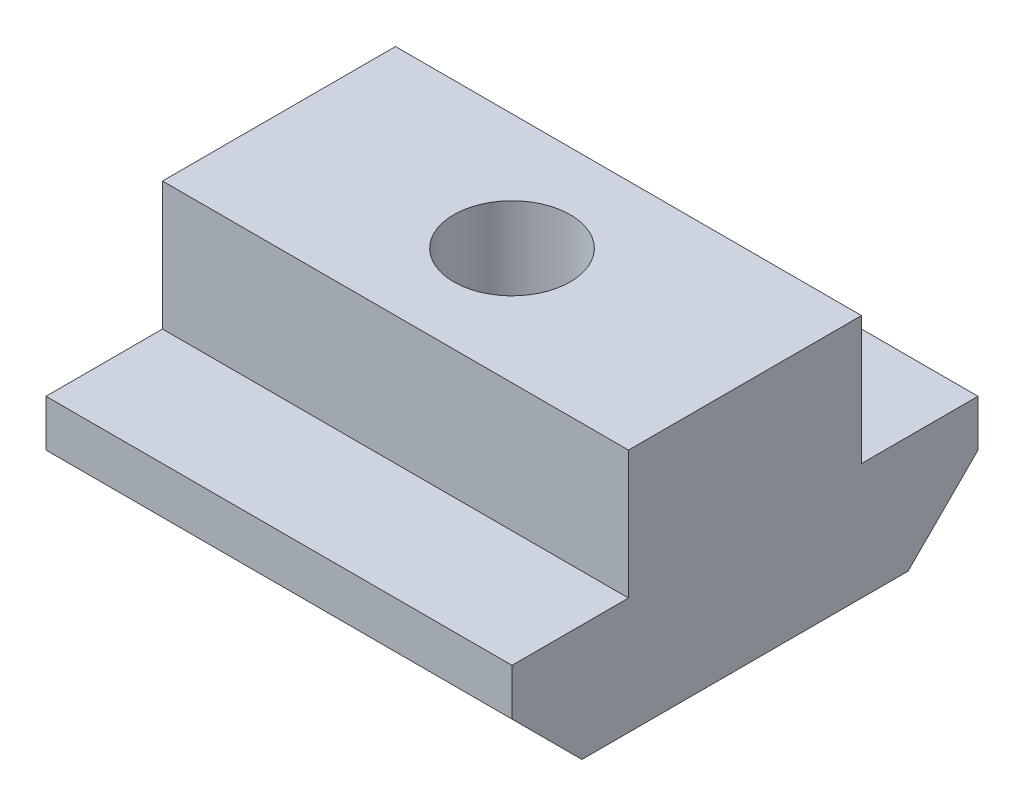
SolidWorks part; units mm, degrees
ref_plane "Спереди" through (0, 0, 0) normal (0, 0, 1) x (1, 0, 0)
ref_plane "Сверху" through (0, 0, 0) normal (0, 1, 0) x (1, 0, 0)
ref_plane "Справа" through (0, 0, 0) normal (1, 0, 0) x (0, 0, -1)
sketch "Эскиз1" plane through (0, 0, 0) normal (1, 0, 0) x (0, 0, -1)
  line L0 (0, 9.2317) -> (-5, 9.2317) construction
  line L1 (-7, -5.25) -> (7, -5.25)
  line L2 (-10, -2.25) -> (-10, -0.25)
  line L3 (-5, 5.25) -> (5, 5.25)
  line L4 (10, -2.25) -> (10, -0.25)
  line L5 (-10, -2.25) -> (-7, -5.25)
  line L6 (7, -5.25) -> (10, -2.25)
  line L7 (-5, 5.25) -> (-5, -0.25)
  line L8 (-5, -0.25) -> (-10, -0.25)
  line L9 (0, 9.2317) -> (5, 9.2317) construction
  line L10 (5, 5.25) -> (5, -0.25)
  line L11 (5, -0.25) -> (10, -0.25)
  point P0 (0, 0)
  point P2 (-10, -5.25)
  point P4 (10, -5.25)
  dimension "D2" = 20
  dimension "D3" = 5
  dimension "D4" = 5.5
  dimension "D5" = 5
  dimension "D6" = 5.5
extrude "Бобышка-Вытянуть1" add sketch "Эскиз1" along normal blind 20
sketch "Эскиз2" plane through (0, 5.25, 0) normal (0, 1, 0) x (1, 0, 0)
  circle A0 centre (10, 0) radius 2.5
  dimension "D1" = 5
extrude "Вырез-Вытянуть1" cut sketch "Эскиз2" against normal through all
